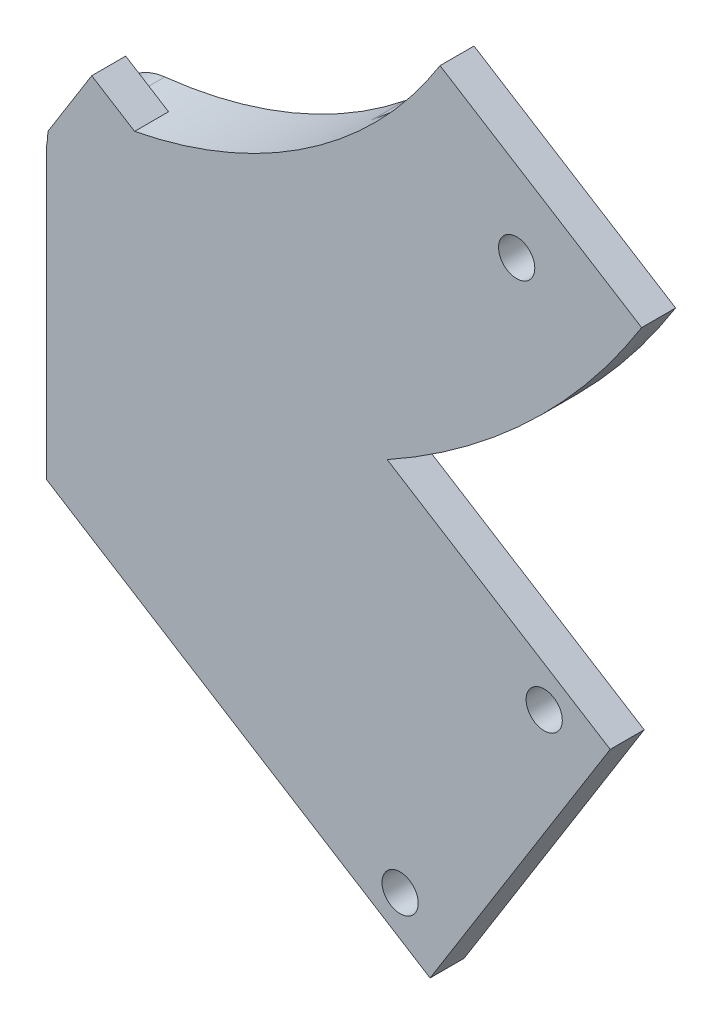
SolidWorks part; units mm, degrees
ref_plane "前视基准面" through (0, 0, 0) normal (0, 0, 1) x (1, 0, 0)
ref_plane "上视基准面" through (0, 0, 0) normal (0, 1, 0) x (1, 0, 0)
ref_plane "右视基准面" through (0, 0, 0) normal (1, 0, 0) x (0, 0, -1)
sketch "草图1" plane through (0, 0, 0) normal (0, 0, 1) x (1, 0, 0)
  line L0 (-20.3043, -30.0134) -> (-20.3043, -51.0134)
  line L1 (8.687, -18.0048) -> (23.5363, -32.854)
  arc A0 (-20.3043, -30.0134) -> (8.687, -18.0048) centre (-20.3043, 10.9866) ccw
  arc A1 (-20.3043, -51.0134) -> (23.5363, -32.854) centre (-20.3043, 10.9866) ccw
  dimension "D1" = 124
  dimension "D2" = 82
  dimension "D3" = 45
extrude "凸台-拉伸1" add sketch "草图1" along normal blind 3
fillet "圆角1" radius 5 4 edges at (-20.3043, -30.0134, 1.5) (-20.3043, -51.0134, 1.5) (23.5363, -32.854, 1.5) (8.687, -18.0048, 1.5)
sketch "草图2" plane through (0, 0, 3) normal (0, 0, 1) x (1, 0, 0)
  line L0 (-20.3043, -30.0134) -> (-20.3043, -51.0134)
  line L1 (14.4588, -10.751) -> (32.2643, -21.885)
  line L2 (19.8454, -29.1631) -> (12.0299, -21.3476) construction
  arc A0 (-20.3043, -30.0134) -> (14.4588, -10.751) centre (-20.3043, 10.9866) ccw
  arc A1 (-20.3043, -51.0134) -> (32.2643, -21.885) centre (-20.3043, 10.9866) ccw
  arc A2 (-20.3043, -42.0888) -> (24.6973, -17.1532) centre (-20.3043, 10.9866) ccw construction
  circle A3 centre (21.2277, -22.0601) radius 1.6
  dimension "D1" = 6
  dimension "D2" = 6
  dimension "D3" = 3.2
extrude "凸台-拉伸2" add sketch "草图2" along normal blind 3
fillet "圆角2" radius 5 2 edges at (-20.3043, -30.0134, 4.5) (-20.3043, -51.0134, 4.5)
sketch "草图3" plane through (0, 0, 6) normal (0, 0, 1) x (1, 0, 0)
  line L0 (-16.2987, -26.9005) -> (29.4869, -55.5305)
  line L1 (32.2643, -21.885) -> (14.4588, -10.751) construction
  line L2 (-16.2987, -26.9005) -> (-20.1599, -33.0752)
  line L3 (-20.3043, -59.778) -> (13.5813, -80.967)
  line L4 (13.5813, -80.967) -> (29.4869, -55.5305)
  line L5 (-13.6499, -32.095) -> (23.6569, -55.4232) construction
  line L6 (23.6569, -55.4232) -> (10.9324, -75.7724) construction
  line L7 (10.9324, -75.7724) -> (-20.3043, -56.2398) construction
  line L8 (-20.3043, -42.7369) -> (-13.6499, -32.095) construction
  line L9 (-20.3043, -34.7409) -> (-20.1599, -33.0752)
  line L13 (-20.3043, -34.7409) -> (-20.3043, -59.778)
  arc A0 (-15.8478, -29.7705) -> (-20.3043, -34.7409) centre (-15.3043, -34.7409) ccw construction
  circle A2 centre (-13.6499, -32.095) radius 1.6
  circle A3 centre (23.6569, -55.4232) radius 1.6
  circle A4 centre (10.9324, -75.7724) radius 1.6
  dimension "D1" = 30
  dimension "D2" = 54
  dimension "D3" = 30
  dimension "D4" = 24
  dimension "D6" = 5
  dimension "D7" = 3
extrude "凸台-拉伸3" add sketch "草图3" against normal blind 3
